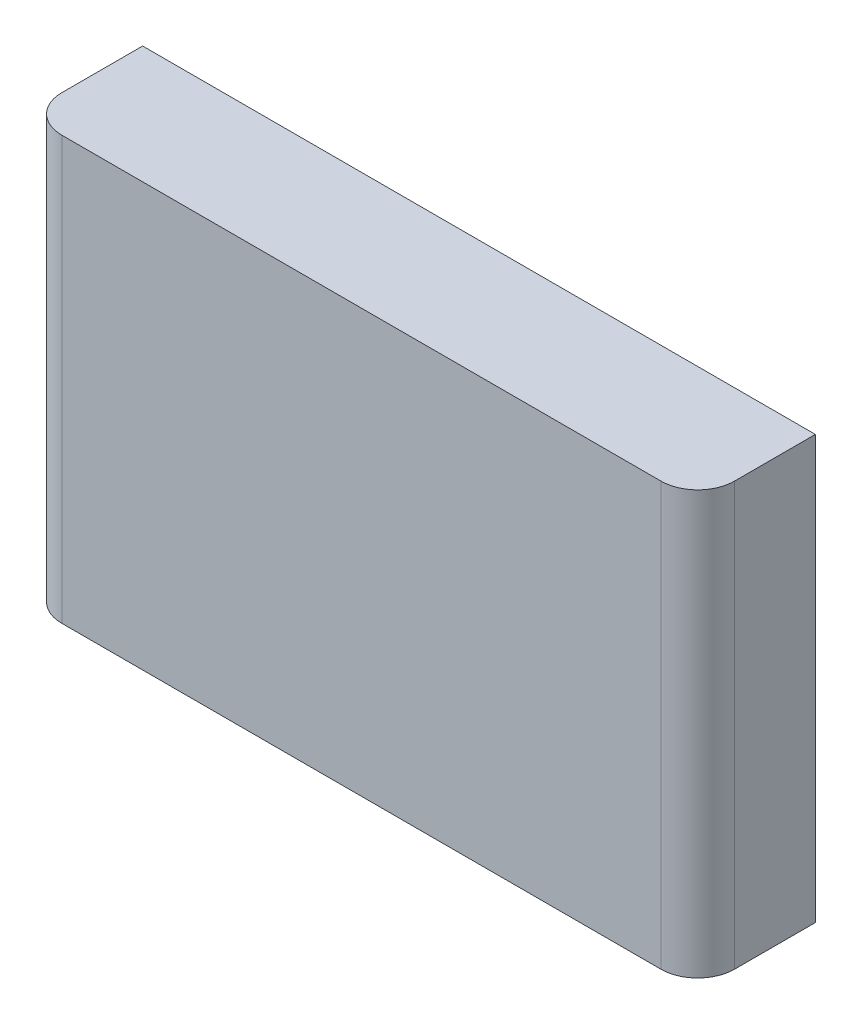
SolidWorks part; units mm, degrees
ref_plane "Ebene vorne" through (0, 0, 0) normal (0, 0, 1) x (1, 0, 0)
ref_plane "Ebene oben" through (0, 0, 0) normal (0, 1, 0) x (1, 0, 0)
ref_plane "Ebene rechts" through (0, 0, 0) normal (1, 0, 0) x (0, 0, -1)
sketch "Sketch1" plane through (0, 0, 0) normal (0, 0, 1) x (1, 0, 0)
  line L1 (45.75, -28.75) -> (-45.75, -28.75)
  line L2 (45.75, -28.75) -> (45.75, 28.75)
  line L3 (45.75, 28.75) -> (-45.75, 28.75)
  line L4 (-45.75, -28.75) -> (-45.75, 28.75)
  line L5 (45.75, -28.75) -> (-45.75, 28.75) construction
  line L6 (45.75, 28.75) -> (-45.75, -28.75) construction
  point P0 (0, 0)
  dimension "D1" = 91.5
  dimension "D2" = 57.5
extrude "Boss-Extrude1" add sketch "Sketch1" along normal blind 16
fillet "Fillet1" radius 5 2 edges at (-45.75, 0, 16) (45.75, 0, 16)
